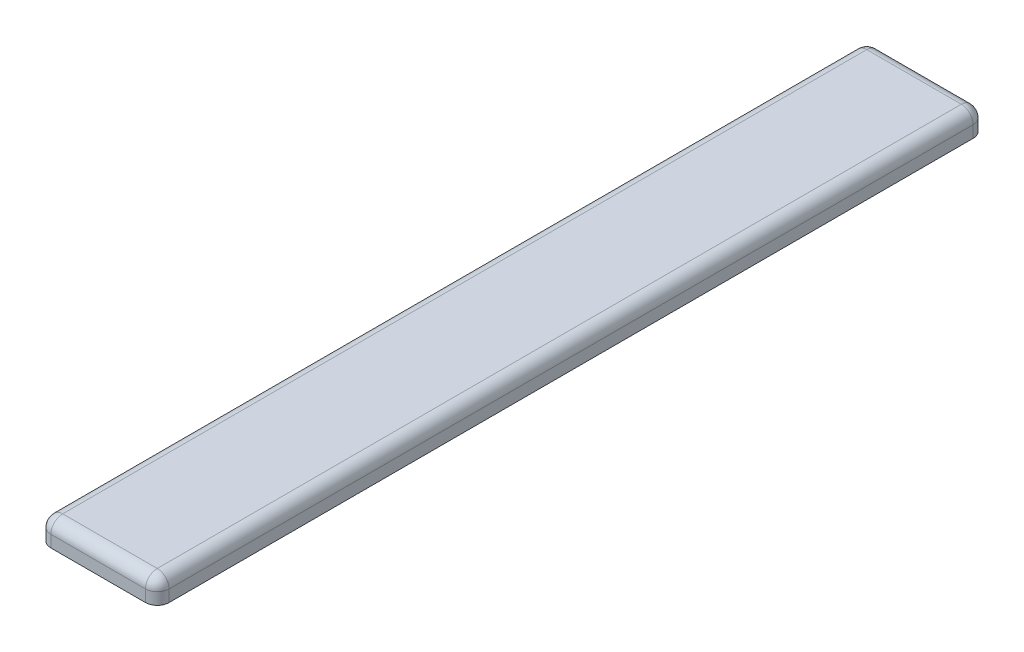
SolidWorks part; units mm, degrees
ref_plane "Front Plane" through (0, 0, 0) normal (0, 0, 1) x (1, 0, 0)
ref_plane "Top Plane" through (0, 0, 0) normal (0, 1, 0) x (1, 0, 0)
ref_plane "Right Plane" through (0, 0, 0) normal (1, 0, 0) x (0, 0, -1)
sketch "Sketch1" plane through (0, 0, 0) normal (0, 1, 0) x (1, 0, 0)
  line L1 (0, 0) -> (100, 0)
  line L2 (0, 0) -> (0, 700)
  line L3 (0, 700) -> (100, 700)
  line L4 (100, 0) -> (100, 700)
  dimension "D1" = 100
  dimension "D2" = 700
extrude "Boss-Extrude1" add sketch "Sketch1" along normal blind 20
fillet "Fillet1" radius 10 8 edges at (50, 20, -700) (100, 20, -350) (50, 20, 0) (0, 20, -350) (100, 10, 0) (0, 10, 0) (100, 10, -700) (0, 10, -700)
